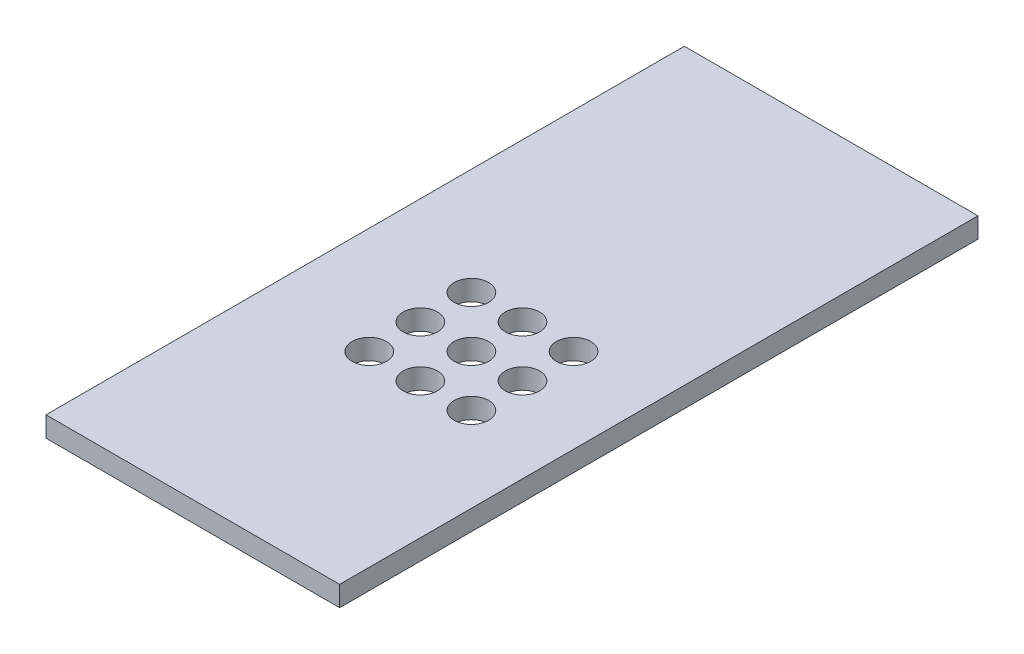
SolidWorks part; units mm, degrees
ref_plane "Front Plane" through (0, 0, 0) normal (0, 0, 1) x (1, 0, 0)
ref_plane "Top Plane" through (0, 0, 0) normal (0, 1, 0) x (1, 0, 0)
ref_plane "Right Plane" through (0, 0, 0) normal (1, 0, 0) x (0, 0, -1)
sketch "Sketch1" plane through (0, 0, 0) normal (0, 1, 0) x (1, 0, 0)
  line L1 (0, 0) -> (23, 0)
  line L2 (0, 0) -> (0, 50)
  line L3 (0, 50) -> (23, 50)
  line L4 (23, 0) -> (23, 50)
  circle A0 centre (8.36, 16.96) radius 1.35
  circle A1 centre (12.36, 16.96) radius 1.35
  circle A2 centre (16.36, 16.96) radius 1.35
  circle A3 centre (8.36, 20.96) radius 1.35
  circle A4 centre (12.36, 20.96) radius 1.35
  circle A5 centre (16.36, 20.96) radius 1.35
  circle A6 centre (8.36, 24.96) radius 1.35
  circle A7 centre (12.36, 24.96) radius 1.35
  circle A8 centre (16.36, 24.96) radius 1.35
  dimension "D1" = 3
  dimension "D2" = 3
extrude "Boss-Extrude1" add sketch "Sketch1" along normal blind 1.5875
